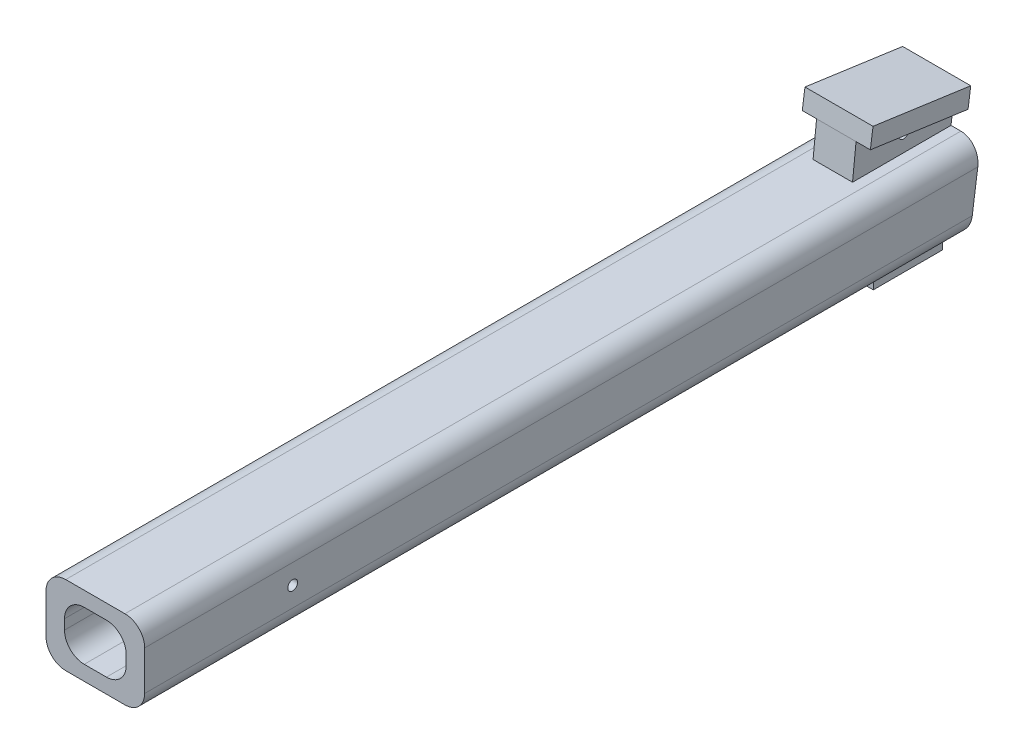
SolidWorks part; units mm, degrees
material "ABS"
ref_plane "Front Plane" through (0, 0, 0) normal (0, 0, 1) x (1, 0, 0)
ref_plane "Top Plane" through (0, 0, 0) normal (0, 1, 0) x (1, 0, 0)
ref_plane "Right Plane" through (0, 0, 0) normal (1, 0, 0) x (0, 0, -1)
sketch "Sketch1" plane through (0, 0, 0) normal (0, 0, 1) x (1, 0, 0)
  line L0 (-6.25, 5) -> (6.25, 5)
  line L1 (-10, 8) -> (10, 8)
  line L2 (-10, 8) -> (-10, -8)
  line L3 (-10, -8) -> (10, -8)
  line L4 (10, 8) -> (10, -8)
  line L5 (-10, 8) -> (10, -8) construction
  line L6 (-10, -8) -> (10, 8) construction
  line L7 (-6.25, 5) -> (-6.25, -5)
  line L8 (6.25, 5) -> (6.25, -5)
  line L9 (-6.25, -5) -> (6.25, -5)
  point P0 (0, 0)
  dimension "D1" = 20
  dimension "D2" = 16
  dimension "D3" = 10
  dimension "D4" = 12.5
extrude "Boss-Extrude1" add sketch "Sketch1" along normal blind 170
fillet "Fillet1" radius 4 4 edges at (10, 8, 85) (10, -8, 85) (-10, 8, 85) (-10, -8, 85)
fillet "Fillet2" radius 4 4 edges at (-6.25, -5, 85) (-6.25, 5, 85) (6.25, 5, 85) (6.25, -5, 85)
sketch "Sketch5" plane through (-10, 0, 0) normal (-1, 0, 0) x (0, 0, 1)
  line L0 (170, 4) -> (170, -4) construction
  line L1 (170, 4) -> (0, 4) construction
  circle A0 centre (140, 0) radius 1
  dimension "D3" = 2
  dimension "D1" = 30
  dimension "D2" = 4
extrude "Cut-Extrude2" cut sketch "Sketch5" against normal through all
sketch "Sketch6" plane through (0, 0, 0) normal (1, 0, 0) x (0, 0, -1)
  line L0 (-170, 8) -> (0, 8) construction
  line L1 (0, 8) -> (-20.5183, 8)
  line L2 (0, 8) -> (0, 12)
  line L3 (0, 12) -> (-19.8054, 14.7835)
  line L4 (-20.5183, 8) -> (-19.8054, 14.7835)
  dimension "D1" = 4
  dimension "D2" = 82
  dimension "D3" = 20
  dimension "D4" = 6
extrude "Boss-Extrude2" add sketch "Sketch6" along normal blind 4 and the other way blind 4
sketch "Sketch7" plane through (0, 11.7676, -1.6538) normal (0, 0.9903, -0.1392) x (1, 0, 0)
  line L1 (-6.9, -1.6701) -> (6.9, -1.6701)
  line L2 (-6.9, -1.6701) -> (-6.9, -21.6701)
  line L3 (-6.9, -21.6701) -> (6.9, -21.6701)
  line L4 (6.9, -1.6701) -> (6.9, -21.6701)
  line L5 (-4, -1.6701) -> (4, -1.6701) construction
  line L6 (-4, -21.6701) -> (4, -21.6701) construction
  line L7 (-4, -1.6701) -> (-4, -21.6701) construction
  line L8 (4, -1.6701) -> (4, -21.6701) construction
  dimension "D1" = 2.9
  dimension "D2" = 2.9
extrude "Boss-Extrude3" add sketch "Sketch7" along normal blind 3.9
sketch "Sketch8" plane through (-6.9, 0, 0) normal (-1, 0, 0) x (0, 0, 1)
  line L0 (0, 12) -> (19.8054, 14.7835) construction
  line L1 (-0.5428, 15.862) -> (0, 12) construction
  circle A0 centre (10.181, 11.4112) radius 1
  dimension "D1" = 2
  dimension "D2" = 2
  dimension "D3" = 10
extrude "Cut-Extrude3" cut sketch "Sketch8" against normal through all
sketch "Sketch9" plane through (10, 0, 0) normal (1, 0, 0) x (0, 0, -1)
  line L0 (0.5428, 15.862) -> (-3.3758, -12.0204)
  line L1 (0.5428, 15.862) -> (0, 12) construction
  line L2 (-3.3758, -12.0204) -> (9.6726, -8.8359)
  line L3 (9.6726, -8.8359) -> (6.2376, 16.6637)
  line L4 (6.2376, 16.6637) -> (0.5428, 15.862)
extrude "Cut-Extrude4" cut sketch "Sketch9" against normal through all
sketch "Sketch10" plane through (0, -8, 0) normal (0, -1, 0) x (1, 0, 0)
  line L0 (-6, 2.8108) -> (6, 2.8108) construction
  line L1 (4.5, 2.8108) -> (-4.5, 2.8108)
  line L2 (4.5, 2.8108) -> (4.5, 16.8108)
  line L3 (4.5, 16.8108) -> (-4.5, 16.8108)
  line L4 (-4.5, 2.8108) -> (-4.5, 16.8108)
  line L5 (0, 0) -> (0, 5.6216) construction
  point P9 (0, 2.8108)
  dimension "D1" = 9
  dimension "D2" = 14
extrude "Boss-Extrude4" add sketch "Sketch10" along normal blind 4.5
sketch "Sketch11" plane through (0, 0, 16.8108) normal (0, 0, 1) x (1, 0, 0)
  line L0 (4.5, -8) -> (-4.5, -8) construction
  line L1 (-2.6, -8) -> (2.6, -8)
  line L2 (-2.6, -8) -> (-2.6, -11.2)
  line L3 (-2.6, -11.2) -> (2.6, -11.2)
  line L4 (2.6, -8) -> (2.6, -11.2)
  point P6 (0, -8)
  dimension "D1" = 5.2
  dimension "D2" = 3.2
extrude "Cut-Extrude5" cut sketch "Sketch11" against normal through all
sketch "Sketch12" plane through (0, -12.5, 0) normal (0, -1, 0) x (1, 0, 0)
  line L0 (-4.5, 2.8108) -> (4.5, 2.8108) construction
  line L1 (-0.8207, 6.1644) -> (0.8207, 6.1644)
  line L2 (-0.8207, 6.1644) -> (-0.8207, -0.5428)
  line L3 (-0.8207, -0.5428) -> (0.8207, -0.5428)
  line L4 (0.8207, 6.1644) -> (0.8207, -0.5428)
  line L5 (-0.8207, 6.1644) -> (0.8207, -0.5428) construction
  line L6 (-0.8207, -0.5428) -> (0.8207, 6.1644) construction
  line L7 (6.9, -0.5428) -> (-6.9, -0.5428) construction
  point P0 (0, 2.8108)
extrude "Boss-Extrude5" add sketch "Sketch12" along normal blind 2
